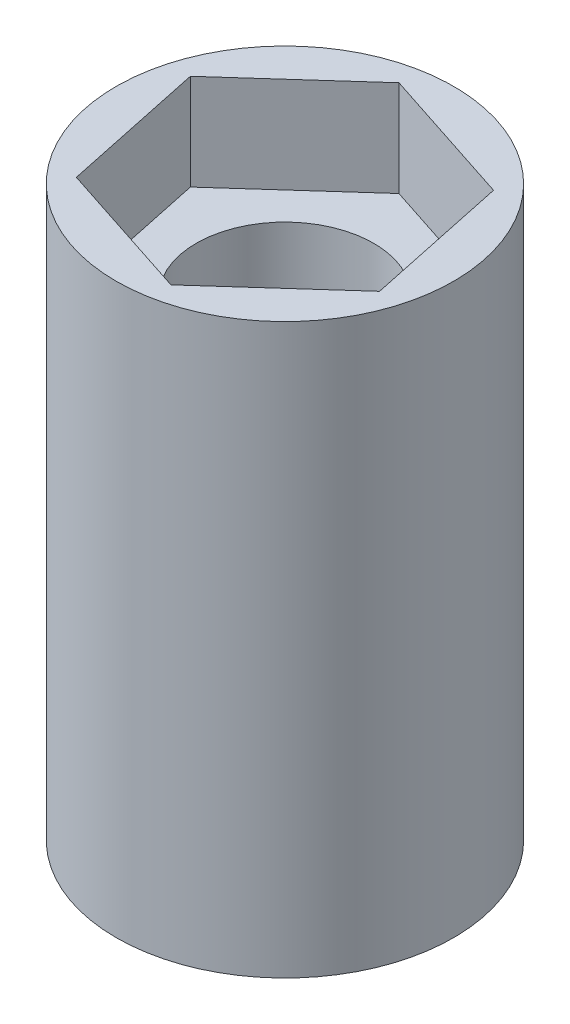
SolidWorks part; units mm, degrees
ref_plane "Ebene vorne" through (0, 0, 0) normal (0, 0, 1) x (1, 0, 0)
ref_plane "Ebene oben" through (0, 0, 0) normal (0, 1, 0) x (1, 0, 0)
ref_plane "Ebene rechts" through (0, 0, 0) normal (1, 0, 0) x (0, 0, -1)
sketch "Skizze1" plane through (0, 0, 0) normal (0, 1, 0) x (1, 0, 0)
  circle A0 centre (0, 0) radius 2.5
  circle A1 centre (0, 0) radius 4.75
  dimension "D1" = 5
  dimension "D2" = 9.5
extrude "Aufsatz-Linear austragen1" add sketch "Skizze1" along normal blind 16
sketch "Skizze2" plane through (0, 16, 0) normal (0, 1, 0) x (1, 0, 0)
  line L1 (3.0929, 2.7774) -> (-0.8588, 4.0672)
  line L2 (-0.8588, 4.0672) -> (-3.9517, 1.2898)
  line L3 (-3.9517, 1.2898) -> (-3.0929, -2.7774)
  line L4 (-3.0929, -2.7774) -> (0.8588, -4.0672)
  line L5 (0.8588, -4.0672) -> (3.9517, -1.2898)
  line L6 (3.9517, -1.2898) -> (3.0929, 2.7774)
  circle A0 centre (0, 0) radius 3.6 construction
  dimension "D1" = 7.2
extrude "Schnitt-Linear austragen1" cut sketch "Skizze2" against normal blind 2.7
